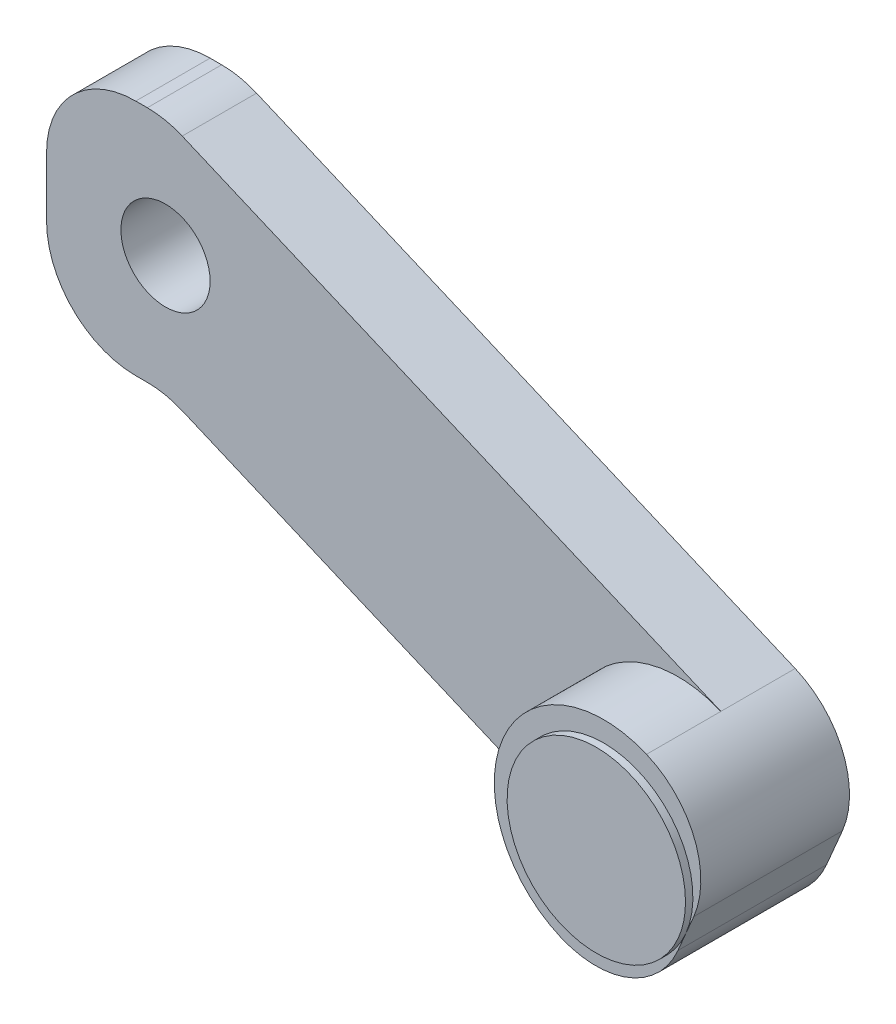
SolidWorks part; units mm, degrees
ref_plane "Plano frontal" through (0, 0, 0) normal (0, 0, 1) x (1, 0, 0)
ref_plane "Plano superior" through (0, 0, 0) normal (0, 1, 0) x (1, 0, 0)
ref_plane "Plano direito" through (0, 0, 0) normal (1, 0, 0) x (0, 0, -1)
sketch "Esboço1" plane through (0, 0, 0) normal (0, 0, 1) x (1, 0, 0)
  line L0 (-8, -8) -> (-8, 8)
  line L5 (-8, 8) -> (0, 8)
  line L6 (0, 8) -> (42.8798, -10.2239)
  line L7 (42.8798, -10.2239) -> (37.1202, -23.7761)
  line L8 (37.1202, -23.7761) -> (0, -8)
  line L9 (0, -8) -> (-8, -8)
  line L10 (-17.8615, 0) -> (30.3176, 0) construction
  circle A0 centre (0, 0) radius 3
  point P0 (0, 0)
  point P14 (40, -17)
  dimension "D3" = 6
  dimension "D1" = 8
  dimension "D2" = 8
  dimension "D4" = 17
  dimension "D5" = 40
extrude "Ressalto-extrusão1" add sketch "Esboço1" along normal blind 5 contours L5 L6 L7 L8 L9 L0 | A0
fillet "Filete1" radius 6 6 edges at (0, -8, 2.5) (-8, -8, 2.5) (-8, 8, 2.5) (0, 8, 2.5) (42.8798, -10.2239, 2.5) (37.1202, -23.7761, 2.5)
sketch "Esboço2" plane through (0, 0, 5) normal (0, 0, 1) x (1, 0, 0)
  line L3 (39.467, -18.2541) -> (40.533, -15.7459)
  line L4 (39.467, -18.2541) -> (40.533, -15.7459)
  arc A4 (37.3578, -7.8771) -> (35.7183, -7.3957) centre (34.478, -14.6532) ccw
  arc A5 (35.7183, -7.3957) -> (31.5982, -21.4292) centre (34.478, -14.6532) ccw
  arc A6 (31.5982, -21.4292) -> (39.467, -18.2541) centre (33.945, -15.9072) ccw
  arc A7 (40.533, -15.7459) -> (37.3578, -7.8771) centre (35.011, -13.3991) ccw
  arc A8 (31.5982, -21.4292) -> (39.467, -18.2541) centre (33.945, -15.9072) ccw
  arc A9 (40.533, -15.7459) -> (37.3578, -7.8771) centre (35.011, -13.3991) ccw
  dimension "D1" = 0
extrude "Ressalto-extrusão2" add sketch "Esboço2" along normal blind 5
sketch "Esboço3" plane through (0, 0, 10) normal (0, 0, 1) x (1, 0, 0)
  circle A0 centre (34.478, -14.6532) radius 6
  arc A1 (37.3578, -7.8771) -> (31.5982, -21.4292) centre (34.478, -14.6532) ccw construction
  dimension "D1" = 12
extrude "Ressalto-extrusão3" add sketch "Esboço3" along normal blind 0.5
